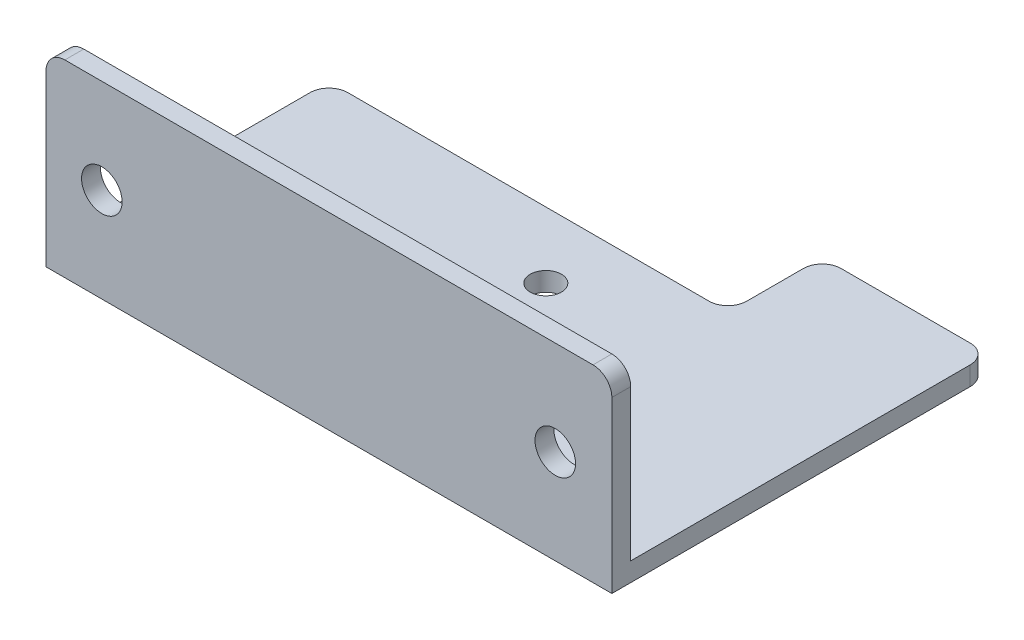
SolidWorks part; units mm, degrees
ref_plane "前视基准面" through (0, 0, 0) normal (0, 0, 1) x (1, 0, 0)
ref_plane "上视基准面" through (0, 0, 0) normal (0, 1, 0) x (1, 0, 0)
ref_plane "右视基准面" through (0, 0, 0) normal (1, 0, 0) x (0, 0, -1)
other "Configuration Table"
sketch "草图1" plane through (0, 0, 0) normal (0, 1, 0) x (1, 0, 0)
  line L1 (-30, -15) -> (30, -15)
  line L2 (-30, -15) -> (-30, 15)
  line L3 (-30, 15) -> (30, 15)
  line L4 (30, -15) -> (30, 15)
  line L5 (0, 15) -> (0, -15) construction
  line L6 (-30, 0) -> (30, 0) construction
  circle A0 centre (0, 8) radius 1.65
  circle A1 centre (0, -8) radius 1.65
  circle A2 centre (8, 0) radius 1.65
  circle A3 centre (-8, 0) radius 1.65
  point P0 (0, 0)
  point P12 (0, 0)
  point P13 (0, 0)
  point P14 (0, 0)
  dimension "D3" = 3.3
  dimension "D5" = 16
  dimension "D7" = 3.3
  dimension "D9" = 3.3
  dimension "D13" = 3.3
  dimension "D1" = 60
  dimension "D2" = 30
  dimension "D4" = 7
  dimension "D6" = 16
  dimension "D8" = 30
  dimension "D10" = 15
  dimension "D11" = 22
  dimension "D12" = 15
extrude "凸台-拉伸3" add sketch "草图1" along normal blind 2 contours A1 | A2 | A0 | A3 | L3 L4 L1 L2
sketch "草图3" plane through (0, 0, 15) normal (0, 0, 1) x (1, 0, 0)
  line L0 (-30, 0) -> (30, 0)
  line L1 (-30, 0) -> (-30, 20)
  line L2 (30, 0) -> (30, 20)
  line L3 (-30, 20) -> (30, 20)
  circle A0 centre (24, 10) radius 2.15
  circle A1 centre (-24.08, 10) radius 2.15
  dimension "D2" = 4.3
  dimension "D4" = 4.3
  dimension "D1" = 20
  dimension "D3" = 10
  dimension "D5" = 48.08
  dimension "D6" = 6
  dimension "D7" = 10
extrude "凸台-拉伸4" add sketch "草图3" against normal blind 2 contours A0 | A1 | L3 L2 L0 L1
sketch "草图4" plane through (0, 2, 0) normal (0, 1, 0) x (1, 0, 0)
  line L1 (30, 15) -> (12.3047, 15)
  line L2 (30, 15) -> (30, 25)
  line L3 (30, 25) -> (12.3047, 25)
  line L4 (12.3047, 15) -> (12.3047, 25)
  dimension "D1" = 10
  dimension "D2" = 17.6953
extrude "凸台-拉伸5" add sketch "草图4" against normal blind 2 contours L4 L3 L2 L1
fillet "圆角1" radius 2 1 edges at (30, 1, -25)
fillet "圆角2" radius 2 1 edges at (12.3047, 1, -25)
fillet "圆角3" radius 2 1 edges at (12.3047, 1, -15)
fillet "圆角4" radius 2 1 edges at (-30, 1, -15)
fillet "圆角5" radius 2 1 edges at (-30, 20, 14)
fillet "圆角6" radius 2 1 edges at (30, 20, 14)
